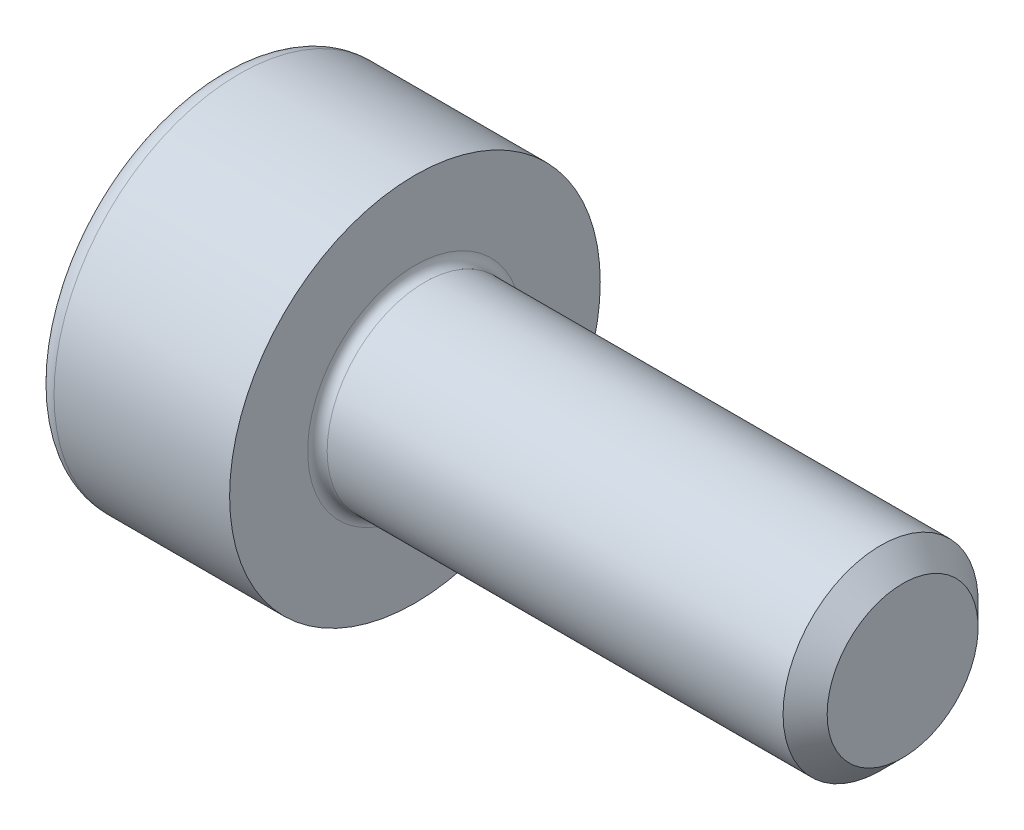
SolidWorks part; units mm, degrees
revolve "Base-Revolve" add sketch "BodySke"
sketch "BodySke" plane through (0, 0, 0) normal (0, 0, 1) x (1, 0, 0)
  line L0 (0, 0) -> (0, 1.9)
  line L1 (0, 1.9) -> (2, 1.9)
  line L2 (2, 1.9) -> (2, 1)
  line L3 (2, 1) -> (6.774, 1)
  line L4 (7, 0.774) -> (7, 0)
  line L5 (7, 0) -> (0, 0)
  line L6 (-31.75, 0) -> (127, 0) construction
  line L8 (7, 0.774) -> (6.774, 1)
  line L10 (7, -0.774) -> (6.774, -1) construction
  line L11 (2.4, 9.525) -> (2.4, 3.175) construction
  line L12 (2, 9.525) -> (2, 3.175) construction
  line L13 (-53, 9.525) -> (-53, 3.175) construction
  dimension "Head_ht" = 2
  dimension "Length" = 5
  dimension "Body_ch_ang" = 45
  dimension "Diameter" = 2
  dimension "Minor_dia" = 1.548
  dimension "Advance" = 0.4
  dimension "Thread_nom" = 5
  dimension "Thread_length" = 60
  dimension "Head_dia" = 3.8
cosmetic thread "ThreadCosmetic" [suppressed]
fillet "Fillet1" radius 0.1 1 edges at (2, 0, 1)
fillet "Fillet2" radius 0.2 1 edges at (0, 0, 1.9)
ref_plane "Plane1" through (0, 0, 0) normal (0, 0, 1) x (1, 0, 0)
ref_plane "Plane2" through (0, 0, 0) normal (0, 1, 0) x (1, 0, 0)
ref_plane "Plane3" through (0, 0, 0) normal (1, 0, 0) x (0, 0, -1)
other "Configuration Table"
sketch "Sketch2" plane through (0, 0, 0) normal (0, 0, 1) x (1, 0, 0)
  line L0 (0, 0.76) -> (1, 0.76)
  line L1 (1, 0.76) -> (1.4388, 0)
  line L2 (-31.75, 0) -> (127, 0) construction
  line L3 (1.4388, 0) -> (0, 0)
  line L4 (0, 0) -> (0, 0.76)
  line L6 (0, 0) -> (47.625, 0) construction
  dimension "D1" = 0.76
  dimension "D2" = 60
  dimension "Depth" = 1
revolve "Hex-PreBroach" cut sketch "Sketch2" angle 360 about L6
sketch "Sketch3" plane through (0, 0, 0) normal (-1, 0, 0) x (0, 0.5, 0.866)
  line L0 (0.4388, 0.76) -> (-0.4388, 0.76)
  line L1 (-0.4388, 0.76) -> (-0.8776, 0)
  line L2 (0.4388, 0.76) -> (0.8776, 0)
  line L3 (0.4388, -0.76) -> (0.8776, 0)
  line L4 (0.4388, -0.76) -> (-0.4388, -0.76)
  line L5 (-0.4388, -0.76) -> (-0.8776, 0)
  dimension "D1" = 0.76
  dimension "D2" = 0.76
  dimension "Hex_size" = 1.52
extrude "Hex" cut sketch "Sketch3" against normal blind 1
sketch "ThdSchSke" plane through (0, 0, 0) normal (0, 0, 1) x (1, 0, 0)
  line L0 (3.2, -0.774) -> (3.0418, -1)
  line L1 (3.2, -0.774) -> (3.3582, -1)
  line L2 (3.3582, -1) -> (3.3582, -1.25)
  line L3 (-3.175, 0) -> (5.1513, 0) construction
  line L4 (0, 1.7) -> (0, -1.7) construction
  line L5 (3.3582, -1.25) -> (3.0418, -1.25)
  line L6 (3.0418, -1.25) -> (3.0418, -1)
  dimension "Thread_minor" = 1.548
  dimension "Diameter" = 2
  dimension "Start" = 3.2
revolve "ThreadSchematic" [suppressed] cut sketch "ThdSchSke" angle 360 about L3
pattern_linear "ThdSchPat" [suppressed]
equation "\"D2@Sketch3\" = \"Hex_size@Sketch3\" / 2"
equation "\"D1@Sketch3\" = \"Hex_size@Sketch3\" / 2"
equation "\"D1@Sketch2\" = \"Hex_size@Sketch3\" / 2"
equation "\"Thread_minor@ThreadCosmetic\"  =  \"Minor_dia@BodySke\""
equation "\"Depth@Sketch2\" =  \"Key_eng@Hex\""
equation "\"Thread_length@ThreadCosmetic\" = ((sgn( (\"Length@BodySke\" - \"Advance@BodySke\" * 3.0) - \"Thread_nom@BodySke\" )-1)*( (\"Length@BodySke\" - \"Advance@BodySke\" * 3.0) - \"Thread_nom@BodySke\" ))/-2+ \"Thread_nom@BodySke\""
equation "\"Thread_minor@ThdSchSke\" = \"Minor_dia@BodySke\""
equation "\"Diameter@ThdSchSke\" = \"Diameter@BodySke\""
equation "\"Overcut@ThdSchSke\" = \"Diameter@BodySke\" * 1.25"
equation "\"Start@ThdSchSke\" = \"Head_ht@BodySke\" + \"Length@BodySke\" - \"Thread_length@ThreadCosmetic\"  '---Non-countersunk---"
equation "\"Num_threads@ThdSchPat\" = int( \"Thread_length@ThreadCosmetic\" / \"Advance@BodySke\" + 0.999 )  + 1"
equation "\"Advance@ThdSchPat\" = \"Thread_length@ThreadCosmetic\" /  (\"Num_threads@ThdSchPat\" - 1) 'relax it"
equation "\"Num_threads@ThdSchPat\" = \"Num_threads@ThdSchPat\" - sgn( \"Num_threads@ThdSchPat\" - 1) '---chamfered tips only---"
